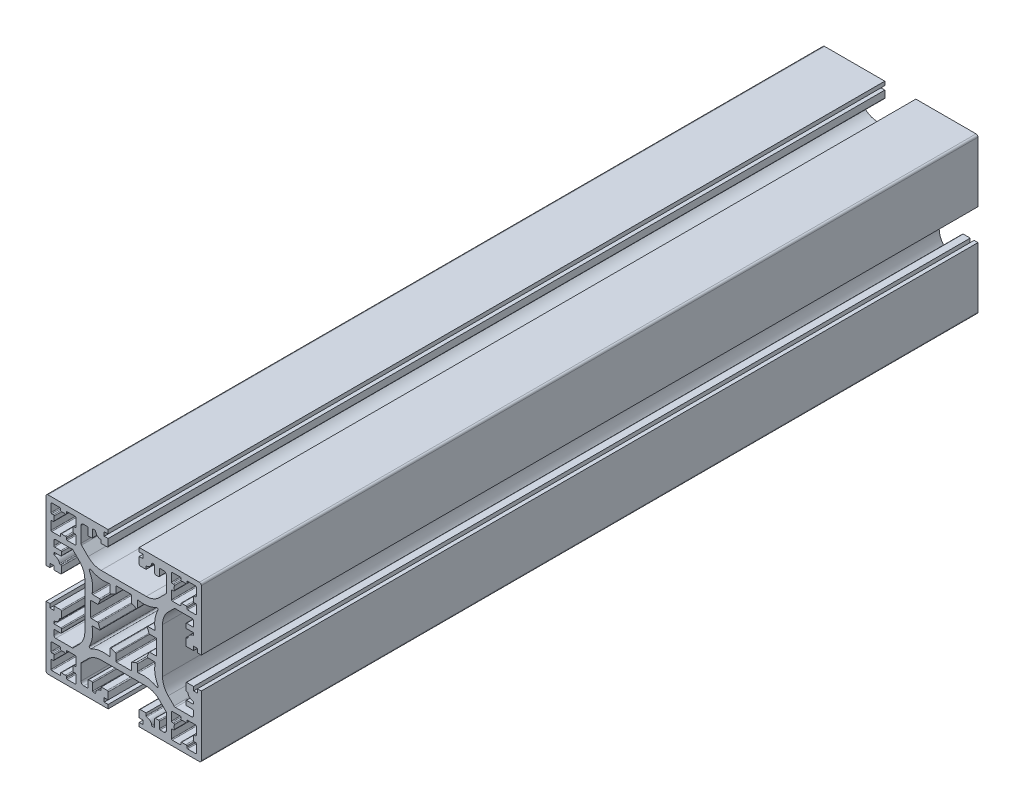
SolidWorks part; units mm, degrees
ref_plane "Front Plane" through (0, 0, 0) normal (0, 0, 1) x (1, 0, 0)
ref_plane "Top Plane" through (0, 0, 0) normal (0, 1, 0) x (1, 0, 0)
ref_plane "Right Plane" through (0, 0, 0) normal (1, 0, 0) x (0, 0, -1)
sketch "Sketch1" plane through (0, 0, 0) normal (0, 0, 1) x (1, 0, 0)
  line L0 (0, -10) -> (0, 10) construction
  line L1 (10, 0) -> (-10, 0) construction
  line L2 (-18, 9.4) -> (-18, 10.5)
  line L3 (-17.8, 9.2) -> (-16.2, 9.2)
  line L4 (-10.8536, 13.0784) -> (-9.1664, 11.3912)
  line L5 (-12.9749, 10.8536) -> (-11.4645, 9.3431)
  line L6 (-7.8, 18.2) -> (-7.4153, 18.2)
  line L7 (-17.8, 8) -> (-16.2, 8)
  line L8 (1.8, 8.5) -> (-1.8, 8.5)
  line L9 (-8.5, 1.8) -> (-8.5, -1.8)
  line L10 (-5.7751, 16) -> (-4.25, 16)
  line L11 (-16, 9) -> (-16, 8.2)
  line L12 (-19.5, 19.5) -> (0, 0) construction
  line L13 (-9.2, 17.8) -> (-9.2, 16.2)
  line L14 (-9, 16) -> (-8.2, 16)
  line L15 (-3.5, 7.9199) -> (-3.5, 6.23)
  line L16 (-2, 8.3) -> (-2, 6.6979)
  line L17 (-15.5, 18.7) -> (-15.5, 12.3) construction
  line L18 (-8, 18) -> (-8, 16.2)
  line L19 (-18.5, 18.7) -> (-16.45, 18.7)
  line L20 (-10.3, 18) -> (-9.4, 18)
  line L21 (-18.7, 18.5) -> (-18.7, 16.45)
  line L22 (-18.5, 12.3) -> (-16.45, 12.3)
  line L23 (-12.3, 18.5) -> (-12.3, 16.45)
  line L24 (-4, 18) -> (-4, 16.25)
  line L25 (-4, 19) -> (-5, 19)
  line L26 (-16.25, 18.1434) -> (-16.25, 18.5)
  line L27 (-14.75, 18.1434) -> (-14.75, 18.5)
  line L28 (-12.8566, 16.25) -> (-12.5, 16.25)
  line L29 (-4, 18) -> (-5, 18)
  line L30 (-12.8566, 14.75) -> (-12.5, 14.75)
  line L31 (-18.1434, 16.25) -> (-18.5, 16.25)
  line L32 (-5, 19) -> (-5, 18)
  line L33 (-18.5, 14.75) -> (-18.1434, 14.75)
  line L34 (-16.25, 12.8566) -> (-16.25, 12.5)
  line L35 (-14.75, 12.8566) -> (-14.75, 12.5)
  line L36 (-16.5, 4) -> (-16.2, 4)
  line L37 (-18, 7.5318) -> (-18, 7.8)
  line L38 (-17.5, 11) -> (-16.25, 11)
  line L39 (-19, 4) -> (-19.5, 4)
  line L40 (-16, 4.2) -> (-16, 4.5)
  line L41 (-19, 4) -> (-19, 5)
  line L42 (-19, 5) -> (-18, 5)
  line L43 (-18, 4) -> (-18, 5)
  line L44 (-16.2, 5.9867) -> (-16.3302, 5.9867)
  line L45 (-5.7751, 16) -> (-5.7751, 16.6365)
  line L46 (-14.55, 18.7) -> (-12.5, 18.7)
  line L47 (-18.7, 14.55) -> (-18.7, 12.5)
  line L48 (-10, -5.8076) -> (-10, 5.8076)
  line L49 (-14.55, 12.3) -> (-12.5, 12.3)
  line L50 (-13.3284, 11) -> (-16.25, 11)
  line L51 (-16, 5.7867) -> (-16, 4.5)
  line L52 (-16.5, 4) -> (-18, 4)
  line L53 (-20, 4.5) -> (-20, 19.5)
  line L54 (-19.5, 20) -> (-4, 20)
  line L55 (-4, 20) -> (-4, 19)
  line L56 (-12.3, 14.55) -> (-12.3, 12.5)
  line L57 (-11, 17.3) -> (-11, 13.432)
  line L58 (-7.9199, 3.5) -> (-6.23, 3.5)
  line L59 (-5.8076, 10) -> (5.8076, 10)
  line L60 (-8.3, 2) -> (-6.6979, 2)
  line L61 (15.5, 18.7) -> (15.5, 12.3) construction
  line L62 (19.5, 19.5) -> (0, 0) construction
  line L63 (20, 4) -> (19.5, 4)
  line L64 (20, 4.5) -> (20, 4)
  line L65 (8.3, 2) -> (6.6979, 2)
  line L66 (7.9199, 3.5) -> (6.23, 3.5)
  line L67 (11, 17.3) -> (11, 13.432)
  line L68 (12.3, 14.55) -> (12.3, 12.5)
  line L69 (4, 20) -> (4, 19)
  line L70 (19.5, 20) -> (4, 20)
  line L71 (20, 4.5) -> (20, 19.5)
  line L72 (16.5, 4) -> (18, 4)
  line L73 (16, 5.7867) -> (16, 4.5)
  line L74 (13.3284, 11) -> (16.25, 11)
  line L75 (14.55, 12.3) -> (12.5, 12.3)
  line L76 (10, -5.8076) -> (10, 5.8076)
  line L77 (18.7, 14.55) -> (18.7, 12.5)
  line L78 (14.55, 18.7) -> (12.5, 18.7)
  line L79 (5.7751, 16) -> (5.7751, 16.6365)
  line L80 (16.2, 5.9867) -> (16.3302, 5.9867)
  line L81 (18, 4) -> (18, 5)
  line L82 (19, 5) -> (18, 5)
  line L83 (19, 4) -> (19, 5)
  line L84 (16, 4.2) -> (16, 4.5)
  line L85 (19, 4) -> (19.5, 4)
  line L86 (17.5, 11) -> (16.25, 11)
  line L87 (18, 7.5318) -> (18, 7.8)
  line L88 (16.5, 4) -> (16.2, 4)
  line L89 (14.75, 12.8566) -> (14.75, 12.5)
  line L90 (16.25, 12.8566) -> (16.25, 12.5)
  line L91 (18.5, 14.75) -> (18.1434, 14.75)
  line L92 (5, 19) -> (5, 18)
  line L93 (18.1434, 16.25) -> (18.5, 16.25)
  line L94 (12.8566, 14.75) -> (12.5, 14.75)
  line L95 (4, 18) -> (5, 18)
  line L96 (12.8566, 16.25) -> (12.5, 16.25)
  line L97 (14.75, 18.1434) -> (14.75, 18.5)
  line L98 (16.25, 18.1434) -> (16.25, 18.5)
  line L99 (4, 19) -> (5, 19)
  line L100 (4, 18) -> (4, 16.25)
  line L101 (12.3, 18.5) -> (12.3, 16.45)
  line L102 (18.5, 12.3) -> (16.45, 12.3)
  line L103 (18.7, 18.5) -> (18.7, 16.45)
  line L104 (10.3, 18) -> (9.4, 18)
  line L105 (18.5, 18.7) -> (16.45, 18.7)
  line L106 (8, 18) -> (8, 16.2)
  line L107 (2, 8.3) -> (2, 6.6979)
  line L108 (3.5, 7.9199) -> (3.5, 6.23)
  line L109 (9, 16) -> (8.2, 16)
  line L110 (9.2, 17.8) -> (9.2, 16.2)
  line L111 (16, 9) -> (16, 8.2)
  line L112 (5.7751, 16) -> (4.25, 16)
  line L113 (8.5, 1.8) -> (8.5, -1.8)
  line L114 (17.8, 8) -> (16.2, 8)
  line L115 (7.8, 18.2) -> (7.4153, 18.2)
  line L116 (12.9749, 10.8536) -> (11.4645, 9.3431)
  line L117 (10.8536, 13.0784) -> (9.1664, 11.3912)
  line L118 (17.8, 9.2) -> (16.2, 9.2)
  line L119 (18, 9.4) -> (18, 10.5)
  line L120 (19.5, -19.5) -> (0, 0) construction
  line L121 (15.5, -18.7) -> (15.5, -12.3) construction
  line L122 (-15.5, -18.7) -> (-15.5, -12.3) construction
  line L123 (-19.5, -19.5) -> (0, 0) construction
  line L124 (-20, -4) -> (-19.5, -4)
  line L125 (-20, -4.5) -> (-20, -4)
  line L126 (18, -9.4) -> (18, -10.5)
  line L127 (17.8, -9.2) -> (16.2, -9.2)
  line L128 (10.8536, -13.0784) -> (9.1664, -11.3912)
  line L129 (12.9749, -10.8536) -> (11.4645, -9.3431)
  line L130 (7.8, -18.2) -> (7.4153, -18.2)
  line L131 (17.8, -8) -> (16.2, -8)
  line L132 (5.7751, -16) -> (4.25, -16)
  line L133 (16, -9) -> (16, -8.2)
  line L134 (9.2, -17.8) -> (9.2, -16.2)
  line L135 (9, -16) -> (8.2, -16)
  line L136 (3.5, -7.9199) -> (3.5, -6.23)
  line L137 (2, -8.3) -> (2, -6.6979)
  line L138 (8, -18) -> (8, -16.2)
  line L139 (18.5, -18.7) -> (16.45, -18.7)
  line L140 (10.3, -18) -> (9.4, -18)
  line L141 (18.7, -18.5) -> (18.7, -16.45)
  line L142 (18.5, -12.3) -> (16.45, -12.3)
  line L143 (12.3, -18.5) -> (12.3, -16.45)
  line L144 (4, -18) -> (4, -16.25)
  line L145 (4, -19) -> (5, -19)
  line L146 (-20, 4.5) -> (-20, 4)
  line L147 (-20, 4) -> (-19.5, 4)
  line L148 (16.25, -18.1434) -> (16.25, -18.5)
  line L149 (14.75, -18.1434) -> (14.75, -18.5)
  line L150 (12.8566, -16.25) -> (12.5, -16.25)
  line L151 (4, -18) -> (5, -18)
  line L152 (12.8566, -14.75) -> (12.5, -14.75)
  line L153 (18.1434, -16.25) -> (18.5, -16.25)
  line L154 (5, -19) -> (5, -18)
  line L155 (18.5, -14.75) -> (18.1434, -14.75)
  line L156 (16.25, -12.8566) -> (16.25, -12.5)
  line L157 (14.75, -12.8566) -> (14.75, -12.5)
  line L158 (16.5, -4) -> (16.2, -4)
  line L159 (18, -7.5318) -> (18, -7.8)
  line L160 (17.5, -11) -> (16.25, -11)
  line L161 (19, -4) -> (19.5, -4)
  line L162 (16, -4.2) -> (16, -4.5)
  line L163 (19, -4) -> (19, -5)
  line L164 (19, -5) -> (18, -5)
  line L165 (18, -4) -> (18, -5)
  line L166 (16.2, -5.9867) -> (16.3302, -5.9867)
  line L167 (5.7751, -16) -> (5.7751, -16.6365)
  line L168 (14.55, -18.7) -> (12.5, -18.7)
  line L169 (18.7, -14.55) -> (18.7, -12.5)
  line L170 (14.55, -12.3) -> (12.5, -12.3)
  line L171 (13.3284, -11) -> (16.25, -11)
  line L172 (16, -5.7867) -> (16, -4.5)
  line L173 (16.5, -4) -> (18, -4)
  line L174 (20, -4.5) -> (20, -19.5)
  line L175 (19.5, -20) -> (4, -20)
  line L176 (4, -20) -> (4, -19)
  line L177 (12.3, -14.55) -> (12.3, -12.5)
  line L178 (11, -17.3) -> (11, -13.432)
  line L179 (7.9199, -3.5) -> (6.23, -3.5)
  line L180 (8.3, -2) -> (6.6979, -2)
  line L181 (20, -4.5) -> (20, -4)
  line L182 (20, -4) -> (19.5, -4)
  line L183 (-8.3, -2) -> (-6.6979, -2)
  line L184 (-5.8076, -10) -> (5.8076, -10)
  line L185 (-7.9199, -3.5) -> (-6.23, -3.5)
  line L186 (-11, -17.3) -> (-11, -13.432)
  line L187 (-12.3, -14.55) -> (-12.3, -12.5)
  line L188 (-4, -20) -> (-4, -19)
  line L189 (-19.5, -20) -> (-4, -20)
  line L190 (-20, -4.5) -> (-20, -19.5)
  line L191 (-16.5, -4) -> (-18, -4)
  line L192 (-16, -5.7867) -> (-16, -4.5)
  line L193 (-13.3284, -11) -> (-16.25, -11)
  line L194 (-14.55, -12.3) -> (-12.5, -12.3)
  line L195 (-18.7, -14.55) -> (-18.7, -12.5)
  line L196 (-14.55, -18.7) -> (-12.5, -18.7)
  line L197 (-5.7751, -16) -> (-5.7751, -16.6365)
  line L198 (-16.2, -5.9867) -> (-16.3302, -5.9867)
  line L199 (-18, -4) -> (-18, -5)
  line L200 (-19, -5) -> (-18, -5)
  line L201 (-19, -4) -> (-19, -5)
  line L202 (-16, -4.2) -> (-16, -4.5)
  line L203 (-19, -4) -> (-19.5, -4)
  line L204 (-17.5, -11) -> (-16.25, -11)
  line L205 (-18, -7.5318) -> (-18, -7.8)
  line L206 (-16.5, -4) -> (-16.2, -4)
  line L207 (-14.75, -12.8566) -> (-14.75, -12.5)
  line L208 (-16.25, -12.8566) -> (-16.25, -12.5)
  line L209 (-18.5, -14.75) -> (-18.1434, -14.75)
  line L210 (-5, -19) -> (-5, -18)
  line L211 (-18.1434, -16.25) -> (-18.5, -16.25)
  line L212 (-12.8566, -14.75) -> (-12.5, -14.75)
  line L213 (-4, -18) -> (-5, -18)
  line L214 (-12.8566, -16.25) -> (-12.5, -16.25)
  line L215 (-14.75, -18.1434) -> (-14.75, -18.5)
  line L216 (-16.25, -18.1434) -> (-16.25, -18.5)
  line L217 (-4, -19) -> (-5, -19)
  line L218 (-4, -18) -> (-4, -16.25)
  line L219 (-12.3, -18.5) -> (-12.3, -16.45)
  line L220 (-18.5, -12.3) -> (-16.45, -12.3)
  line L221 (-18.7, -18.5) -> (-18.7, -16.45)
  line L222 (-10.3, -18) -> (-9.4, -18)
  line L223 (-18.5, -18.7) -> (-16.45, -18.7)
  line L224 (-8, -18) -> (-8, -16.2)
  line L225 (-2, -8.3) -> (-2, -6.6979)
  line L226 (-3.5, -7.9199) -> (-3.5, -6.23)
  line L227 (-9, -16) -> (-8.2, -16)
  line L228 (-9.2, -17.8) -> (-9.2, -16.2)
  line L229 (-16, -9) -> (-16, -8.2)
  line L230 (-5.7751, -16) -> (-4.25, -16)
  line L231 (1.8, -8.5) -> (-1.8, -8.5)
  line L232 (-17.8, -8) -> (-16.2, -8)
  line L233 (-7.8, -18.2) -> (-7.4153, -18.2)
  line L234 (-12.9749, -10.8536) -> (-11.4645, -9.3431)
  line L235 (-10.8536, -13.0784) -> (-9.1664, -11.3912)
  line L236 (-17.8, -9.2) -> (-16.2, -9.2)
  line L237 (-18, -9.4) -> (-18, -10.5)
  arc A0 (-2.1376, 6.5079) -> (-3.2064, 6.0532) centre (0, 0) ccw
  arc A1 (-6.0532, 3.2064) -> (-6.5079, 2.1376) centre (0, 0) ccw
  arc A2 (-8.1161, 3.7385) -> (-8.8345, 8.4277) centre (-14.9853, 5.0858) ccw
  arc A3 (-8.4277, 8.8345) -> (-3.7385, 8.1161) centre (-5.0858, 14.9853) ccw
  arc A4 (-8.8345, 8.4277) -> (-8.4277, 8.8345) centre (-8.5709, 8.5709) cw
  arc A5 (-3.5, 6.23) -> (-3.2064, 6.0532) centre (-3.3, 6.23) ccw
  arc A6 (-17.9476, 16.0093) -> (-17.9476, 14.9907) centre (-15.5, 15.5) ccw
  arc A7 (-2, 6.6979) -> (-2.1376, 6.5079) centre (-2.2, 6.6979) cw
  arc A8 (-2, 8.3) -> (-1.8, 8.5) centre (-1.8, 8.3) cw
  arc A9 (-3.5, 7.9199) -> (-3.7385, 8.1161) centre (-3.7, 7.9199) ccw
  arc A10 (-6.23, 3.5) -> (-6.0532, 3.2064) centre (-6.23, 3.3) cw
  arc A11 (-7.9199, 3.5) -> (-8.1161, 3.7385) centre (-7.9199, 3.7) cw
  arc A12 (-6.6979, 2) -> (-6.5079, 2.1376) centre (-6.6979, 2.2) ccw
  arc A13 (-8.3, 2) -> (-8.5, 1.8) centre (-8.3, 1.8) ccw
  arc A14 (9.4, 18) -> (9.2, 17.8) centre (9.4, 17.8) ccw
  arc A15 (9.2, 16.2) -> (9, 16) centre (9, 16.2) cw
  arc A16 (-17.8234, 7.3332) -> (-16.5259, 6.1458) centre (-18, 5.8376) cw
  arc A17 (-7.217, 18.0255) -> (-5.9605, 16.8359) centre (-5.8604, 18.2) ccw
  arc A18 (-14.9907, 17.9476) -> (-16.0093, 17.9476) centre (-15.5, 15.5) ccw
  arc A19 (-13.0524, 14.9907) -> (-13.0524, 16.0093) centre (-15.5, 15.5) ccw
  arc A20 (-16.0093, 13.0524) -> (-14.9907, 13.0524) centre (-15.5, 15.5) ccw
  arc A21 (-14.75, 12.8566) -> (-14.9907, 13.0524) centre (-14.95, 12.8566) ccw
  arc A22 (-16.25, 12.8566) -> (-16.0093, 13.0524) centre (-16.05, 12.8566) cw
  arc A23 (-4, 16.25) -> (-4.25, 16) centre (-4.25, 16.25) cw
  arc A24 (-16.25, 12.5) -> (-16.45, 12.3) centre (-16.45, 12.5) cw
  arc A25 (-14.75, 12.5) -> (-14.55, 12.3) centre (-14.55, 12.5) ccw
  arc A26 (-12.5, 14.75) -> (-12.3, 14.55) centre (-12.5, 14.55) cw
  arc A27 (-12.8566, 14.75) -> (-13.0524, 14.9907) centre (-12.8566, 14.95) cw
  arc A28 (-10.3, 18) -> (-11, 17.3) centre (-10.3, 17.3) ccw
  arc A29 (-9.1664, 11.3912) -> (-5.8076, 10) centre (-5.8076, 14.75) ccw
  arc A30 (-10, 5.8076) -> (-11.4645, 9.3431) centre (-15, 5.8076) ccw
  arc A31 (-10.8536, 13.0784) -> (-11, 13.432) centre (-10.5, 13.432) cw
  arc A32 (-12.9749, 10.8536) -> (-13.3284, 11) centre (-13.3284, 10.5) ccw
  arc A33 (-18, 10.5) -> (-17.5, 11) centre (-17.5, 10.5) cw
  arc A34 (-12.8566, 16.25) -> (-13.0524, 16.0093) centre (-12.8566, 16.05) ccw
  arc A35 (-12.5, 16.25) -> (-12.3, 16.45) centre (-12.5, 16.45) ccw
  arc A36 (-12.5, 12.3) -> (-12.3, 12.5) centre (-12.5, 12.5) ccw
  arc A37 (-12.5, 18.7) -> (-12.3, 18.5) centre (-12.5, 18.5) cw
  arc A38 (-20, 19.5) -> (-19.5, 20) centre (-19.5, 19.5) cw
  arc A39 (-14.75, 18.5) -> (-14.55, 18.7) centre (-14.55, 18.5) cw
  arc A40 (-14.75, 18.1434) -> (-14.9907, 17.9476) centre (-14.95, 18.1434) cw
  arc A41 (-16.25, 18.1434) -> (-16.0093, 17.9476) centre (-16.05, 18.1434) ccw
  arc A42 (-16.25, 18.5) -> (-16.45, 18.7) centre (-16.45, 18.5) ccw
  arc A43 (-18.5, 18.7) -> (-18.7, 18.5) centre (-18.5, 18.5) ccw
  arc A44 (-18.5, 16.25) -> (-18.7, 16.45) centre (-18.5, 16.45) cw
  arc A45 (-18.1434, 16.25) -> (-17.9476, 16.0093) centre (-18.1434, 16.05) cw
  arc A46 (-18.1434, 14.75) -> (-17.9476, 14.9907) centre (-18.1434, 14.95) ccw
  arc A47 (-18.5, 14.75) -> (-18.7, 14.55) centre (-18.5, 14.55) ccw
  arc A48 (-18.7, 12.5) -> (-18.5, 12.3) centre (-18.5, 12.5) ccw
  arc A49 (-16, 5.7867) -> (-16.2, 5.9867) centre (-16.2, 5.7867) ccw
  arc A50 (-16.3302, 5.9867) -> (-16.5259, 6.1458) centre (-16.3302, 6.1867) cw
  arc A51 (-16.2, 4) -> (-16, 4.2) centre (-16.2, 4.2) ccw
  arc A52 (-18, 7.5318) -> (-17.8234, 7.3332) centre (-17.8, 7.5318) ccw
  arc A53 (-18, 7.8) -> (-17.8, 8) centre (-17.8, 7.8) cw
  arc A54 (-16.2, 8) -> (-16, 8.2) centre (-16.2, 8.2) ccw
  arc A55 (-16.2, 9.2) -> (-16, 9) centre (-16.2, 9) cw
  arc A56 (-17.8, 9.2) -> (-18, 9.4) centre (-17.8, 9.4) cw
  arc A57 (-5.7751, 16.6365) -> (-5.9605, 16.8359) centre (-5.9751, 16.6365) ccw
  arc A58 (-7.4153, 18.2) -> (-7.217, 18.0255) centre (-7.4153, 18) cw
  arc A59 (-7.8, 18.2) -> (-8, 18) centre (-7.8, 18) ccw
  arc A60 (-8.2, 16) -> (-8, 16.2) centre (-8.2, 16.2) ccw
  arc A61 (-9.2, 16.2) -> (-9, 16) centre (-9, 16.2) ccw
  arc A62 (-9.4, 18) -> (-9.2, 17.8) centre (-9.4, 17.8) cw
  arc A63 (8.2, 16) -> (8, 16.2) centre (8.2, 16.2) cw
  arc A64 (7.8, 18.2) -> (8, 18) centre (7.8, 18) cw
  arc A65 (7.4153, 18.2) -> (7.217, 18.0255) centre (7.4153, 18) ccw
  arc A66 (5.7751, 16.6365) -> (5.9605, 16.8359) centre (5.9751, 16.6365) cw
  arc A67 (17.8, 9.2) -> (18, 9.4) centre (17.8, 9.4) ccw
  arc A68 (16.2, 9.2) -> (16, 9) centre (16.2, 9) ccw
  arc A69 (16.2, 8) -> (16, 8.2) centre (16.2, 8.2) cw
  arc A70 (18, 7.8) -> (17.8, 8) centre (17.8, 7.8) ccw
  arc A71 (18, 7.5318) -> (17.8234, 7.3332) centre (17.8, 7.5318) cw
  arc A72 (16.2, 4) -> (16, 4.2) centre (16.2, 4.2) cw
  arc A73 (16.3302, 5.9867) -> (16.5259, 6.1458) centre (16.3302, 6.1867) ccw
  arc A74 (16, 5.7867) -> (16.2, 5.9867) centre (16.2, 5.7867) cw
  arc A75 (18.7, 12.5) -> (18.5, 12.3) centre (18.5, 12.5) cw
  arc A76 (18.5, 14.75) -> (18.7, 14.55) centre (18.5, 14.55) cw
  arc A77 (18.1434, 14.75) -> (17.9476, 14.9907) centre (18.1434, 14.95) cw
  arc A78 (18.1434, 16.25) -> (17.9476, 16.0093) centre (18.1434, 16.05) ccw
  arc A79 (18.5, 16.25) -> (18.7, 16.45) centre (18.5, 16.45) ccw
  arc A80 (18.5, 18.7) -> (18.7, 18.5) centre (18.5, 18.5) cw
  arc A81 (16.25, 18.5) -> (16.45, 18.7) centre (16.45, 18.5) cw
  arc A82 (16.25, 18.1434) -> (16.0093, 17.9476) centre (16.05, 18.1434) cw
  arc A83 (14.75, 18.1434) -> (14.9907, 17.9476) centre (14.95, 18.1434) ccw
  arc A84 (14.75, 18.5) -> (14.55, 18.7) centre (14.55, 18.5) ccw
  arc A85 (20, 19.5) -> (19.5, 20) centre (19.5, 19.5) ccw
  arc A86 (12.5, 18.7) -> (12.3, 18.5) centre (12.5, 18.5) ccw
  arc A87 (12.5, 12.3) -> (12.3, 12.5) centre (12.5, 12.5) cw
  arc A88 (12.5, 16.25) -> (12.3, 16.45) centre (12.5, 16.45) cw
  arc A89 (12.8566, 16.25) -> (13.0524, 16.0093) centre (12.8566, 16.05) cw
  arc A90 (18, 10.5) -> (17.5, 11) centre (17.5, 10.5) ccw
  arc A91 (12.9749, 10.8536) -> (13.3284, 11) centre (13.3284, 10.5) cw
  arc A92 (10.8536, 13.0784) -> (11, 13.432) centre (10.5, 13.432) ccw
  arc A93 (10, 5.8076) -> (11.4645, 9.3431) centre (15, 5.8076) cw
  arc A94 (9.1664, 11.3912) -> (5.8076, 10) centre (5.8076, 14.75) cw
  arc A95 (10.3, 18) -> (11, 17.3) centre (10.3, 17.3) cw
  arc A96 (12.8566, 14.75) -> (13.0524, 14.9907) centre (12.8566, 14.95) ccw
  arc A97 (12.5, 14.75) -> (12.3, 14.55) centre (12.5, 14.55) ccw
  arc A98 (14.75, 12.5) -> (14.55, 12.3) centre (14.55, 12.5) cw
  arc A99 (16.25, 12.5) -> (16.45, 12.3) centre (16.45, 12.5) ccw
  arc A100 (4, 16.25) -> (4.25, 16) centre (4.25, 16.25) ccw
  arc A101 (16.25, 12.8566) -> (16.0093, 13.0524) centre (16.05, 12.8566) ccw
  arc A102 (14.75, 12.8566) -> (14.9907, 13.0524) centre (14.95, 12.8566) cw
  arc A103 (16.0093, 13.0524) -> (14.9907, 13.0524) centre (15.5, 15.5) cw
  arc A104 (13.0524, 14.9907) -> (13.0524, 16.0093) centre (15.5, 15.5) cw
  arc A105 (14.9907, 17.9476) -> (16.0093, 17.9476) centre (15.5, 15.5) cw
  arc A106 (7.217, 18.0255) -> (5.9605, 16.8359) centre (5.8604, 18.2) cw
  arc A107 (17.8234, 7.3332) -> (16.5259, 6.1458) centre (18, 5.8376) ccw
  arc A108 (8.3, 2) -> (8.5, 1.8) centre (8.3, 1.8) cw
  arc A109 (6.6979, 2) -> (6.5079, 2.1376) centre (6.6979, 2.2) cw
  arc A110 (7.9199, 3.5) -> (8.1161, 3.7385) centre (7.9199, 3.7) ccw
  arc A111 (6.23, 3.5) -> (6.0532, 3.2064) centre (6.23, 3.3) ccw
  arc A112 (3.5, 7.9199) -> (3.7385, 8.1161) centre (3.7, 7.9199) cw
  arc A113 (2, 8.3) -> (1.8, 8.5) centre (1.8, 8.3) ccw
  arc A114 (2, 6.6979) -> (2.1376, 6.5079) centre (2.2, 6.6979) ccw
  arc A115 (17.9476, 16.0093) -> (17.9476, 14.9907) centre (15.5, 15.5) cw
  arc A116 (3.5, 6.23) -> (3.2064, 6.0532) centre (3.3, 6.23) cw
  arc A117 (8.8345, 8.4277) -> (8.4277, 8.8345) centre (8.5709, 8.5709) ccw
  arc A118 (8.4277, 8.8345) -> (3.7385, 8.1161) centre (5.0858, 14.9853) cw
  arc A119 (8.1161, 3.7385) -> (8.8345, 8.4277) centre (14.9853, 5.0858) cw
  arc A120 (6.0532, 3.2064) -> (6.5079, 2.1376) centre (0, 0) cw
  arc A121 (2.1376, 6.5079) -> (3.2064, 6.0532) centre (0, 0) cw
  arc A122 (2.1376, -6.5079) -> (3.2064, -6.0532) centre (0, 0) ccw
  arc A123 (6.0532, -3.2064) -> (6.5079, -2.1376) centre (0, 0) ccw
  arc A124 (8.1161, -3.7385) -> (8.8345, -8.4277) centre (14.9853, -5.0858) ccw
  arc A125 (8.4277, -8.8345) -> (3.7385, -8.1161) centre (5.0858, -14.9853) ccw
  arc A126 (8.8345, -8.4277) -> (8.4277, -8.8345) centre (8.5709, -8.5709) cw
  arc A127 (3.5, -6.23) -> (3.2064, -6.0532) centre (3.3, -6.23) ccw
  arc A128 (17.9476, -16.0093) -> (17.9476, -14.9907) centre (15.5, -15.5) ccw
  arc A129 (2, -6.6979) -> (2.1376, -6.5079) centre (2.2, -6.6979) cw
  arc A130 (2, -8.3) -> (1.8, -8.5) centre (1.8, -8.3) cw
  arc A131 (3.5, -7.9199) -> (3.7385, -8.1161) centre (3.7, -7.9199) ccw
  arc A132 (6.23, -3.5) -> (6.0532, -3.2064) centre (6.23, -3.3) cw
  arc A133 (7.9199, -3.5) -> (8.1161, -3.7385) centre (7.9199, -3.7) cw
  arc A134 (6.6979, -2) -> (6.5079, -2.1376) centre (6.6979, -2.2) ccw
  arc A135 (8.3, -2) -> (8.5, -1.8) centre (8.3, -1.8) ccw
  arc A136 (17.8234, -7.3332) -> (16.5259, -6.1458) centre (18, -5.8376) cw
  arc A137 (7.217, -18.0255) -> (5.9605, -16.8359) centre (5.8604, -18.2) ccw
  arc A138 (14.9907, -17.9476) -> (16.0093, -17.9476) centre (15.5, -15.5) ccw
  arc A139 (13.0524, -14.9907) -> (13.0524, -16.0093) centre (15.5, -15.5) ccw
  arc A140 (16.0093, -13.0524) -> (14.9907, -13.0524) centre (15.5, -15.5) ccw
  arc A141 (14.75, -12.8566) -> (14.9907, -13.0524) centre (14.95, -12.8566) ccw
  arc A142 (16.25, -12.8566) -> (16.0093, -13.0524) centre (16.05, -12.8566) cw
  arc A143 (4, -16.25) -> (4.25, -16) centre (4.25, -16.25) cw
  arc A144 (16.25, -12.5) -> (16.45, -12.3) centre (16.45, -12.5) cw
  arc A145 (14.75, -12.5) -> (14.55, -12.3) centre (14.55, -12.5) ccw
  arc A146 (12.5, -14.75) -> (12.3, -14.55) centre (12.5, -14.55) cw
  arc A147 (12.8566, -14.75) -> (13.0524, -14.9907) centre (12.8566, -14.95) cw
  arc A148 (10.3, -18) -> (11, -17.3) centre (10.3, -17.3) ccw
  arc A149 (9.1664, -11.3912) -> (5.8076, -10) centre (5.8076, -14.75) ccw
  arc A150 (10, -5.8076) -> (11.4645, -9.3431) centre (15, -5.8076) ccw
  arc A151 (10.8536, -13.0784) -> (11, -13.432) centre (10.5, -13.432) cw
  arc A152 (12.9749, -10.8536) -> (13.3284, -11) centre (13.3284, -10.5) ccw
  arc A153 (18, -10.5) -> (17.5, -11) centre (17.5, -10.5) cw
  arc A154 (12.8566, -16.25) -> (13.0524, -16.0093) centre (12.8566, -16.05) ccw
  arc A155 (12.5, -16.25) -> (12.3, -16.45) centre (12.5, -16.45) ccw
  arc A156 (12.5, -12.3) -> (12.3, -12.5) centre (12.5, -12.5) ccw
  arc A157 (12.5, -18.7) -> (12.3, -18.5) centre (12.5, -18.5) cw
  arc A158 (20, -19.5) -> (19.5, -20) centre (19.5, -19.5) cw
  arc A159 (14.75, -18.5) -> (14.55, -18.7) centre (14.55, -18.5) cw
  arc A160 (14.75, -18.1434) -> (14.9907, -17.9476) centre (14.95, -18.1434) cw
  arc A161 (16.25, -18.1434) -> (16.0093, -17.9476) centre (16.05, -18.1434) ccw
  arc A162 (16.25, -18.5) -> (16.45, -18.7) centre (16.45, -18.5) ccw
  arc A163 (18.5, -18.7) -> (18.7, -18.5) centre (18.5, -18.5) ccw
  arc A164 (18.5, -16.25) -> (18.7, -16.45) centre (18.5, -16.45) cw
  arc A165 (18.1434, -16.25) -> (17.9476, -16.0093) centre (18.1434, -16.05) cw
  arc A166 (18.1434, -14.75) -> (17.9476, -14.9907) centre (18.1434, -14.95) ccw
  arc A167 (18.5, -14.75) -> (18.7, -14.55) centre (18.5, -14.55) ccw
  arc A168 (18.7, -12.5) -> (18.5, -12.3) centre (18.5, -12.5) ccw
  arc A169 (16, -5.7867) -> (16.2, -5.9867) centre (16.2, -5.7867) ccw
  arc A170 (16.3302, -5.9867) -> (16.5259, -6.1458) centre (16.3302, -6.1867) cw
  arc A171 (16.2, -4) -> (16, -4.2) centre (16.2, -4.2) ccw
  arc A172 (18, -7.5318) -> (17.8234, -7.3332) centre (17.8, -7.5318) ccw
  arc A173 (18, -7.8) -> (17.8, -8) centre (17.8, -7.8) cw
  arc A174 (16.2, -8) -> (16, -8.2) centre (16.2, -8.2) ccw
  arc A175 (16.2, -9.2) -> (16, -9) centre (16.2, -9) cw
  arc A176 (17.8, -9.2) -> (18, -9.4) centre (17.8, -9.4) cw
  arc A177 (5.7751, -16.6365) -> (5.9605, -16.8359) centre (5.9751, -16.6365) ccw
  arc A178 (7.4153, -18.2) -> (7.217, -18.0255) centre (7.4153, -18) cw
  arc A179 (7.8, -18.2) -> (8, -18) centre (7.8, -18) ccw
  arc A180 (8.2, -16) -> (8, -16.2) centre (8.2, -16.2) ccw
  arc A181 (-9.4, -18) -> (-9.2, -17.8) centre (-9.4, -17.8) ccw
  arc A182 (-9.2, -16.2) -> (-9, -16) centre (-9, -16.2) cw
  arc A183 (-8.2, -16) -> (-8, -16.2) centre (-8.2, -16.2) cw
  arc A184 (-7.8, -18.2) -> (-8, -18) centre (-7.8, -18) cw
  arc A185 (-7.4153, -18.2) -> (-7.217, -18.0255) centre (-7.4153, -18) ccw
  arc A186 (-5.7751, -16.6365) -> (-5.9605, -16.8359) centre (-5.9751, -16.6365) cw
  arc A187 (-17.8, -9.2) -> (-18, -9.4) centre (-17.8, -9.4) ccw
  arc A188 (-16.2, -9.2) -> (-16, -9) centre (-16.2, -9) ccw
  arc A189 (-16.2, -8) -> (-16, -8.2) centre (-16.2, -8.2) cw
  arc A190 (-18, -7.8) -> (-17.8, -8) centre (-17.8, -7.8) ccw
  arc A191 (-18, -7.5318) -> (-17.8234, -7.3332) centre (-17.8, -7.5318) cw
  arc A192 (-16.2, -4) -> (-16, -4.2) centre (-16.2, -4.2) cw
  arc A193 (-16.3302, -5.9867) -> (-16.5259, -6.1458) centre (-16.3302, -6.1867) ccw
  arc A194 (-16, -5.7867) -> (-16.2, -5.9867) centre (-16.2, -5.7867) cw
  arc A195 (-18.7, -12.5) -> (-18.5, -12.3) centre (-18.5, -12.5) cw
  arc A196 (-18.5, -14.75) -> (-18.7, -14.55) centre (-18.5, -14.55) cw
  arc A197 (-18.1434, -14.75) -> (-17.9476, -14.9907) centre (-18.1434, -14.95) cw
  arc A198 (-18.1434, -16.25) -> (-17.9476, -16.0093) centre (-18.1434, -16.05) ccw
  arc A199 (-18.5, -16.25) -> (-18.7, -16.45) centre (-18.5, -16.45) ccw
  arc A200 (-18.5, -18.7) -> (-18.7, -18.5) centre (-18.5, -18.5) cw
  arc A201 (-16.25, -18.5) -> (-16.45, -18.7) centre (-16.45, -18.5) cw
  arc A202 (-16.25, -18.1434) -> (-16.0093, -17.9476) centre (-16.05, -18.1434) cw
  arc A203 (-14.75, -18.1434) -> (-14.9907, -17.9476) centre (-14.95, -18.1434) ccw
  arc A204 (-14.75, -18.5) -> (-14.55, -18.7) centre (-14.55, -18.5) ccw
  arc A205 (-20, -19.5) -> (-19.5, -20) centre (-19.5, -19.5) ccw
  arc A206 (-12.5, -18.7) -> (-12.3, -18.5) centre (-12.5, -18.5) ccw
  arc A207 (-12.5, -12.3) -> (-12.3, -12.5) centre (-12.5, -12.5) cw
  arc A208 (-12.5, -16.25) -> (-12.3, -16.45) centre (-12.5, -16.45) cw
  arc A209 (-12.8566, -16.25) -> (-13.0524, -16.0093) centre (-12.8566, -16.05) cw
  arc A210 (-18, -10.5) -> (-17.5, -11) centre (-17.5, -10.5) ccw
  arc A211 (-12.9749, -10.8536) -> (-13.3284, -11) centre (-13.3284, -10.5) cw
  arc A212 (-10.8536, -13.0784) -> (-11, -13.432) centre (-10.5, -13.432) ccw
  arc A213 (-10, -5.8076) -> (-11.4645, -9.3431) centre (-15, -5.8076) cw
  arc A214 (-9.1664, -11.3912) -> (-5.8076, -10) centre (-5.8076, -14.75) cw
  arc A215 (-10.3, -18) -> (-11, -17.3) centre (-10.3, -17.3) cw
  arc A216 (-12.8566, -14.75) -> (-13.0524, -14.9907) centre (-12.8566, -14.95) ccw
  arc A217 (-12.5, -14.75) -> (-12.3, -14.55) centre (-12.5, -14.55) ccw
  arc A218 (-14.75, -12.5) -> (-14.55, -12.3) centre (-14.55, -12.5) cw
  arc A219 (-16.25, -12.5) -> (-16.45, -12.3) centre (-16.45, -12.5) ccw
  arc A220 (-4, -16.25) -> (-4.25, -16) centre (-4.25, -16.25) ccw
  arc A221 (-16.25, -12.8566) -> (-16.0093, -13.0524) centre (-16.05, -12.8566) ccw
  arc A222 (-14.75, -12.8566) -> (-14.9907, -13.0524) centre (-14.95, -12.8566) cw
  arc A223 (-16.0093, -13.0524) -> (-14.9907, -13.0524) centre (-15.5, -15.5) cw
  arc A224 (-13.0524, -14.9907) -> (-13.0524, -16.0093) centre (-15.5, -15.5) cw
  arc A225 (-14.9907, -17.9476) -> (-16.0093, -17.9476) centre (-15.5, -15.5) cw
  arc A226 (-7.217, -18.0255) -> (-5.9605, -16.8359) centre (-5.8604, -18.2) cw
  arc A227 (-17.8234, -7.3332) -> (-16.5259, -6.1458) centre (-18, -5.8376) ccw
  arc A228 (9.2, -16.2) -> (9, -16) centre (9, -16.2) ccw
  arc A229 (9.4, -18) -> (9.2, -17.8) centre (9.4, -17.8) cw
  arc A230 (-8.3, -2) -> (-8.5, -1.8) centre (-8.3, -1.8) cw
  arc A231 (-6.6979, -2) -> (-6.5079, -2.1376) centre (-6.6979, -2.2) cw
  arc A232 (-7.9199, -3.5) -> (-8.1161, -3.7385) centre (-7.9199, -3.7) ccw
  arc A233 (-6.23, -3.5) -> (-6.0532, -3.2064) centre (-6.23, -3.3) ccw
  arc A234 (-3.5, -7.9199) -> (-3.7385, -8.1161) centre (-3.7, -7.9199) cw
  arc A235 (-2, -8.3) -> (-1.8, -8.5) centre (-1.8, -8.3) ccw
  arc A236 (-2, -6.6979) -> (-2.1376, -6.5079) centre (-2.2, -6.6979) ccw
  arc A237 (-17.9476, -16.0093) -> (-17.9476, -14.9907) centre (-15.5, -15.5) cw
  arc A238 (-3.5, -6.23) -> (-3.2064, -6.0532) centre (-3.3, -6.23) cw
  arc A239 (-8.8345, -8.4277) -> (-8.4277, -8.8345) centre (-8.5709, -8.5709) ccw
  arc A240 (-8.4277, -8.8345) -> (-3.7385, -8.1161) centre (-5.0858, -14.9853) cw
  arc A241 (-8.1161, -3.7385) -> (-8.8345, -8.4277) centre (-14.9853, -5.0858) cw
  arc A242 (-6.0532, -3.2064) -> (-6.5079, -2.1376) centre (0, 0) cw
  arc A243 (-2.1376, -6.5079) -> (-3.2064, -6.0532) centre (0, 0) cw
  point P4 (9.2, 16)
  point P29 (10.0355, -10.0355)
  point P42 (-10.0355, 10.0355)
  point P53 (-5.8883, 3.5)
  point P92 (-14.75, 13.1152)
  point P102 (-4, 19)
  point P103 (-16.25, 13.1152)
  point P126 (-14.75, 12.3)
  point P129 (-12.3, 14.75)
  point P132 (-13.1152, 14.75)
  point P139 (-12.3, 12.3)
  point P142 (-12.3, 18.7)
  point P145 (-14.75, 18.7)
  point P148 (-14.75, 17.8848)
  point P153 (-16.25, 18.7)
  point P156 (-18.7, 18.7)
  point P161 (-17.8848, 16.25)
  point P166 (-18.7, 14.75)
  point P181 (-16, 8)
  point P184 (-16, 9.2)
  point P195 (-8, 16)
  point P198 (-9.2, 16)
  point P380 (0, 8.5)
  point P381 (8, 16)
  point P382 (16, 9.2)
  point P383 (16, 8)
  point P384 (18.7, 14.75)
  point P385 (17.8848, 16.25)
  point P386 (18.7, 18.7)
  point P387 (16.25, 18.7)
  point P388 (14.75, 17.8848)
  point P389 (14.75, 18.7)
  point P390 (12.3, 18.7)
  point P391 (12.3, 12.3)
  point P392 (13.1152, 14.75)
  point P393 (12.3, 14.75)
  point P394 (14.75, 12.3)
  point P395 (16.25, 13.1152)
  point P396 (14.75, 13.1152)
  point P397 (5.8883, 3.5)
  point P398 (10.0355, 10.0355)
  point P722 (8.5, 0)
  point P751 (-8.5, 0)
  point P752 (5.8883, -3.5)
  point P753 (14.75, -13.1152)
  point P754 (16.25, -13.1152)
  point P755 (14.75, -12.3)
  point P756 (12.3, -14.75)
  point P757 (13.1152, -14.75)
  point P758 (12.3, -12.3)
  point P759 (12.3, -18.7)
  point P760 (14.75, -18.7)
  point P761 (14.75, -17.8848)
  point P762 (16.25, -18.7)
  point P763 (18.7, -18.7)
  point P764 (17.8848, -16.25)
  point P765 (18.7, -14.75)
  point P766 (16, -8)
  point P767 (16, -9.2)
  point P768 (8, -16)
  point P769 (0, -8.5)
  point P770 (-9.2, -16)
  point P771 (-8, -16)
  point P772 (-16, -9.2)
  point P773 (-16, -8)
  point P774 (-18.7, -14.75)
  point P775 (-17.8848, -16.25)
  point P776 (-18.7, -18.7)
  point P777 (-16.25, -18.7)
  point P778 (-14.75, -17.8848)
  point P779 (-14.75, -18.7)
  point P780 (-12.3, -18.7)
  point P781 (-12.3, -12.3)
  point P782 (-13.1152, -14.75)
  point P783 (-12.3, -14.75)
  point P784 (-14.75, -12.3)
  point P785 (-16.25, -13.1152)
  point P786 (-14.75, -13.1152)
  point P787 (-5.8883, -3.5)
  point P788 (-10.0355, -10.0355)
  point P789 (9.2, -16)
extrude "Extrude1" add sketch "Sketch1" against normal blind 200
